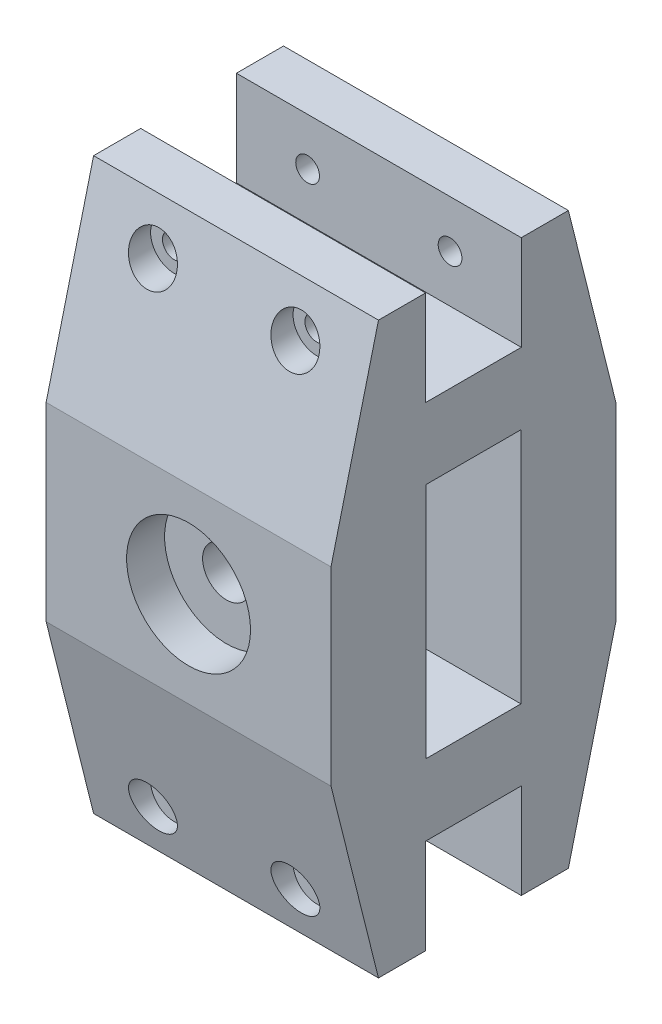
SolidWorks part; units mm, degrees
material "ABS"
ref_plane "Front Plane" through (0, 0, 0) normal (0, 0, 1) x (1, 0, 0)
ref_plane "Top Plane" through (0, 0, 0) normal (0, 1, 0) x (1, 0, 0)
ref_plane "Right Plane" through (0, 0, 0) normal (1, 0, 0) x (0, 0, -1)
sketch "Sketch2" plane through (0, 0, 0) normal (1, 0, 0) x (0, 0, -1)
  line L0 (30, 120) -> (30, 0) construction
  line L1 (0, 0) -> (60, 0)
  line L2 (0, 0) -> (0, 120)
  line L3 (0, 120) -> (60, 120)
  line L4 (60, 0) -> (60, 120)
  line L5 (30, 0) -> (60, 60) construction
  line L6 (60, 60) -> (0, 60) construction
  line L7 (0, 80) -> (10, 120)
  line L8 (60, 80) -> (50, 120)
  line L9 (60, 40) -> (50, 0)
  line L10 (0, 40) -> (10, 0)
  line L11 (19.925, 20) -> (40.075, 20)
  line L12 (19.925, 140) -> (40.075, 140)
  line L13 (19.925, 140) -> (19.925, 100)
  line L14 (19.925, 100) -> (40.075, 100)
  line L15 (40.075, 140) -> (40.075, 100)
  line L16 (19.925, 140) -> (40.075, 100) construction
  line L17 (19.925, 100) -> (40.075, 140) construction
  line L18 (40.075, -20) -> (40.075, 20)
  line L19 (19.925, -20) -> (40.075, -20)
  line L20 (19.925, -20) -> (19.925, 20)
  dimension "D1" = 60
  dimension "D2" = 120
  dimension "D3" = 20
  dimension "D4" = 20
  dimension "D5" = 20.15
  dimension "D6" = 20
extrude "Boss-Extrude1" add sketch "Sketch2" along normal blind 60 contours L2 L10 L1 L9 L4 L8 L3 L7
sketch "Sketch3" plane through (0, 0, 0) normal (0, 0, 1) x (1, 0, 0)
  line L0 (0, 60) -> (60, 60) construction
  line L1 (0, 40) -> (0, 80) construction
  line L2 (60, 40) -> (60, 80) construction
  line L3 (60, 60) -> (30, 120) construction
  line L4 (60, 120) -> (0, 120) construction
  line L5 (30, 120) -> (30, -5.0282) construction
  circle A0 centre (30, 60) radius 5.05
  dimension "D1" = 10.1
extrude "Cut-Extrude1" cut sketch "Sketch3" against normal blind 70
ref_plane "Plane1" through (0, 0, -30) normal (0, 0, 1) x (1, 0, 0)
sketch "Sketch4" plane through (0, 0, 0) normal (0, 0, 1) x (1, 0, 0)
  circle A0 centre (30, 60) radius 13.05
  dimension "D1" = 26.1
extrude "Cut-Extrude2" cut sketch "Sketch4" against normal blind 8
mirror "Mirror1" about plane through (0, 0, -30) normal (0, 0, 1) of "Cut-Extrude2"
sketch "Sketch5" plane through (0, 0, 0) normal (0, 0, 1) x (1, 0, 0)
  line L0 (30, 60) -> (89.4194, 60) construction
  line L1 (89.4194, 60) -> (-15.9572, 60) construction
  line L2 (-15.9572, 60) -> (30, 60) construction
  line L3 (30, 60) -> (30, 132.1461) construction
  line L4 (60, 120) -> (0, 120) construction
  circle A0 centre (45, 110) radius 2.5
  circle A1 centre (15, 110) radius 2.5
  circle A2 centre (45, 10) radius 2.5
  circle A3 centre (15, 10) radius 2.5
  dimension "D1" = 5
  dimension "D2" = 15
  dimension "D3" = 10
extrude "Cut-Extrude3" cut sketch "Sketch5" against normal through all
sketch "Sketch6" plane through (0, 0, 0) normal (0, 0, 1) x (1, 0, 0)
  line L0 (30, 120) -> (30, -1.9963) construction
  line L1 (60, 120) -> (0, 120) construction
  line L2 (30, -1.9963) -> (60, 60) construction
  line L3 (60, 40) -> (60, 80) construction
  line L4 (60, 60) -> (-4.5066, 60) construction
  circle A0 centre (45, 110) radius 500000
  circle A1 centre (45, 110) radius 5
  circle A2 centre (15, 110) radius 5
  circle A3 centre (15, 10) radius 5
  circle A4 centre (45, 10) radius 5
  dimension "D1" = 1000000
  dimension "D2" = 10
extrude "Cut-Extrude4" cut sketch "Sketch6" against normal blind 12 contours A2 | A1 | A3 | A4
mirror "Mirror2" about plane through (0, 0, -30) normal (0, 0, 1) of "Cut-Extrude4"
sketch "Sketch7" plane through (60, 0, 0) normal (1, 0, 0) x (0, 0, -1)
  line L0 (30, 20) -> (30, 100) construction
  line L1 (19.925, 20) -> (40.075, 20) construction
  line L2 (19.925, 100) -> (40.075, 100) construction
  line L3 (30, 100) -> (30, 60) construction
  line L4 (30, 60) -> (85.0304, 60) construction
  line L5 (0, 40) -> (0, 80) construction
  line L6 (20, 35) -> (40, 35)
  line L7 (20, 35) -> (20, 85)
  line L8 (20, 85) -> (40, 85)
  line L9 (40, 35) -> (40, 85)
  line L10 (20, 35) -> (40, 85) construction
  line L11 (20, 85) -> (40, 35) construction
  dimension "D1" = 15
  dimension "D2" = 20
extrude "Cut-Extrude5" cut sketch "Sketch7" against normal blind 81
